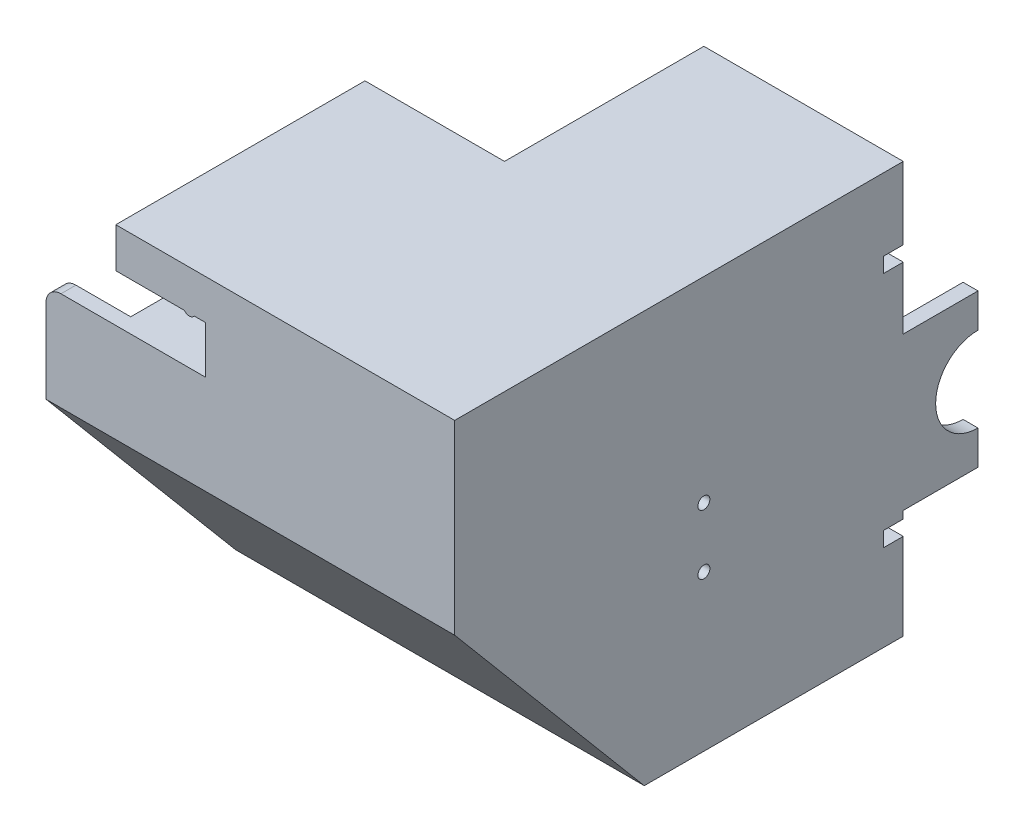
SolidWorks part; units mm, degrees
ref_plane "Front Plane" through (0, 0, 0) normal (0, 0, 1) x (1, 0, 0)
ref_plane "Top Plane" through (0, 0, 0) normal (0, 1, 0) x (1, 0, 0)
ref_plane "Right Plane" through (0, 0, 0) normal (1, 0, 0) x (0, 0, -1)
sketch "Sketch1" plane through (0, 0, 75.0548) normal (0, 0, 1) x (1, 0, 0)
  line L0 (-69.2126, 51.9708) -> (-97.2126, 51.9708)
  line L1 (-97.2126, 51.9708) -> (-97.2126, 43.9708)
  line L2 (-97.2126, 43.9708) -> (-83.4626, 43.9708)
  line L3 (-81.4626, 43.9708) -> (-79.2126, 43.9708)
  line L4 (-79.2126, 43.9708) -> (-79.2126, 34.4708)
  line L5 (-79.2126, 34.4708) -> (-97.2126, 34.4708)
  line L6 (-97.2126, 34.4708) -> (-97.2126, 26.4708)
  line L7 (-97.2126, 26.4708) -> (-69.2126, 26.4708)
  line L8 (-69.2126, 26.4708) -> (-69.2126, 51.9708)
  arc A0 (-83.4626, 43.9708) -> (-81.4626, 43.9708) centre (-82.4626, 44.7208) ccw
  arc A1 (-83.4626, 43.9708) -> (-81.4626, 43.9708) centre (-82.4626, 44.7208) ccw construction
  arc M1 (-83.4626, 43.9708) -> (-81.4626, 43.9708) centre (-82.4626, 44.7208) ccw
  line M2 (-81.4626, 43.9708) -> (-79.2126, 43.9708)
  line M3 (-79.2126, 43.9708) -> (-79.2126, 34.4708)
  line M4 (-79.2126, 34.4708) -> (-97.2126, 34.4708)
  line M5 (-97.2126, 34.4708) -> (-97.2126, 26.4708)
  line M6 (-97.2126, 26.4708) -> (-69.2126, 26.4708)
  line M7 (-69.2126, 26.4708) -> (-69.2126, 51.9708)
  line M8 (-69.2126, 51.9708) -> (-97.2126, 51.9708)
  line M9 (-97.2126, 51.9708) -> (-97.2126, 43.9708)
  line M10 (-97.2126, 43.9708) -> (-83.4626, 43.9708)
extrude "Boss-Extrude1" add sketch "Sketch1" along normal blind 50 contours M10 M1 M2 M3 M4 M5 M6 M7 M8 M9
sketch "Sketch2" plane through (-69.2126, 0, 0) normal (1, 0, 0) x (0, 0, -1)
  line L0 (-125.0548, 51.9708) -> (-35.0548, 51.9708)
  line L1 (-35.0548, 51.9708) -> (-35.0548, 48.9708)
  line L2 (-35.0548, 22.4708) -> (-35.0548, 51.9708) construction
  line L3 (-35.0548, 48.9708) -> (-125.0548, 48.9708)
  line L4 (-125.0548, 26.4708) -> (-125.0548, 51.9708) construction
  line L5 (-125.0548, 48.9708) -> (-125.0548, 51.9708)
  line L6 (-125.0548, 48.9708) -> (-125.0548, 26.4708)
  line L7 (-125.0548, 26.4708) -> (-122.0548, 26.4708)
  line L8 (-125.0548, 26.4708) -> (-75.0548, 26.4708) construction
  line L9 (-122.0548, 26.4708) -> (-122.0548, 48.9708)
  line M3 (-75.0548, 26.4708) -> (-75.0548, 51.9708)
  line M4 (-75.0548, 51.9708) -> (-125.0548, 51.9708)
  line M5 (-125.0548, 51.9708) -> (-125.0548, 26.4708)
  line M6 (-125.0548, 26.4708) -> (-75.0548, 26.4708)
  dimension "D1" = 3
  dimension "D2" = 3
extrude "Boss-Extrude2" add sketch "Sketch2" along normal up to surface (40 mm away) contours L9 L3 M6 M5 | L3 M3 M4 M5 | L3 L1 L0 M3
sketch "Sketch3" plane through (0, 0, 75.0548) normal (0, 0, -1) x (-1, 0, 0)
  line L0 (79.2126, 43.9708) -> (97.2126, 43.9708)
  line L1 (97.2126, 43.9708) -> (97.2126, 34.4708)
  line L2 (97.2126, 34.4708) -> (79.2126, 34.4708)
  line L3 (79.2126, 34.4708) -> (79.2126, 43.9708)
extrude "Cut-Extrude1" cut sketch "Sketch3" against normal blind 30
sketch "Sketch4" plane through (0, 48.9708, 0) normal (0, -1, 0) x (1, 0, 0)
  line L0 (-29.2126, 125.0548) -> (-32.2126, 125.0548)
  line L1 (-97.2126, 125.0548) -> (-29.2126, 125.0548) construction
  line L2 (-32.2126, 125.0548) -> (-32.2126, 35.0548)
  line L3 (-29.2126, 35.0548) -> (-69.2126, 35.0548) construction
  line L4 (-32.2126, 35.0548) -> (-29.2126, 35.0548)
  line L5 (-29.2126, 35.0548) -> (-29.2126, 125.0548)
  dimension "D1" = 3
extrude "Boss-Extrude3" add sketch "Sketch4" along normal up to surface (79.5 mm away)
sketch "Sketch6" plane through (-32.2126, 0, 0) normal (-1, 0, 0) x (0, 0, 1)
  line L0 (125.0548, -30.5292) -> (35.0548, -30.5292)
  line L1 (35.0548, -30.5292) -> (35.0548, -27.5292)
  line L2 (35.0548, -30.5292) -> (35.0548, 48.9708) construction
  line L3 (35.0548, -27.5292) -> (125.0548, -27.5292)
  line L4 (125.0548, -30.5292) -> (125.0548, 26.4708) construction
  line L5 (125.0548, -27.5292) -> (125.0548, -30.5292)
  dimension "D1" = 3
extrude "Boss-Extrude4" add sketch "Sketch6" along normal up to surface (79 mm away)
sketch "Sketch7" plane through (0, 0, 125.0548) normal (0, 0, 1) x (1, 0, 0)
  line L0 (-111.2126, -27.5292) -> (-32.2126, -27.5292)
  line L1 (-32.2126, -27.5292) -> (-32.2126, 26.4708)
  line L2 (-32.2126, 26.4708) -> (-97.2126, 26.4708)
  line L3 (-97.2126, 26.4708) -> (-97.2126, 34.4708)
  line L4 (-97.2126, 34.4708) -> (-111.2126, 34.4708)
  line L5 (-111.2126, 34.4708) -> (-111.2126, -27.5292)
extrude "Boss-Extrude5" add sketch "Sketch7" against normal blind 3
fillet "Fillet1" radius 3 1 edges at (-111.2126, 34.4708, 123.5548)
sketch "Sketch11" plane through (-29.2126, 0, 0) normal (1, 0, 0) x (0, 0, -1)
  line L0 (-35.0548, 34.4708) -> (-39.0548, 34.4708)
  line L1 (-35.0548, 51.9708) -> (-35.0548, -30.5292) construction
  line L2 (-35.0548, 28.4708) -> (-35.0548, 34.4708) construction
  line L3 (-39.0548, 34.4708) -> (-39.0548, 37.4708)
  line L4 (-39.0548, 37.4708) -> (-35.0548, 37.4708)
  line L5 (-35.0548, 37.4708) -> (-35.0548, 34.4708)
  line L6 (-75.0548, 34.4708) -> (-25.0548, 34.4708) construction
  dimension "D1" = 3
  dimension "D2" = 4
extrude "Cut-Extrude2" cut sketch "Sketch11" against normal up to surface (3 mm away) up to face at (-32.2126, 10.7208, 78.5548)
sketch "Sketch12" plane through (0, -30.5292, 0) normal (0, -1, 0) x (1, 0, 0)
  line L0 (-111.2126, 35.0548) -> (-29.2126, 35.0548)
  line L1 (-69.2126, 35.0548) -> (-69.2126, 75.0548)
  line L2 (-70.7126, 39.0548) -> (-67.7126, 39.0548)
  line L3 (-67.7126, 39.0548) -> (-67.7126, 35.0548)
  line L4 (-67.7126, 35.0548) -> (-70.7126, 35.0548)
  line L5 (-70.7126, 35.0548) -> (-70.7126, 39.0548)
  line L6 (-75.2126, 75.0548) -> (-63.2126, 75.0548)
  circle A0 centre (-75.2126, 75.0548) radius 1.2
  circle A1 centre (-63.2126, 75.0548) radius 1.2
  point P10 (-69.2126, 39.0548)
  point P14 (-69.2126, 75.0548)
  dimension "D5" = 2.4
  dimension "D6" = 2.4
  dimension "D1" = 40
  dimension "D2" = 4
  dimension "D3" = 3
  dimension "D4" = 12
sketch "Sketch13" plane through (-29.2126, 0, 0) normal (1, 0, 0) x (0, 0, -1)
  line L0 (-5.0548, 22.4708) -> (-5.0548, -9.1792)
  line L1 (-5.0548, 6.6458) -> (-20.0548, 6.6458)
  line L2 (-5.0548, 22.4708) -> (-35.0548, 22.4708)
  line L3 (-35.0548, 22.4708) -> (-35.0548, -9.1792)
  line L4 (-35.0548, -9.1792) -> (-5.0548, -9.1792)
  line L5 (-20.0548, -9.1792) -> (-20.0548, 22.4708)
  line L6 (-20.0548, 21.9708) -> (-35.0548, 21.9708)
  line L7 (-20.0548, -8.6792) -> (-35.0548, -8.6792)
  circle A0 centre (-20.0548, 6.6458) radius 8.5
  point P9 (-20.0548, 6.6458)
  point P16 (-5.0548, 22.4708)
  dimension "D1" = 17
  dimension "D2" = 15
  dimension "D3" = 0.5
  dimension "D4" = 0.5
extrude "Boss-Extrude6" add sketch "Sketch13" against normal blind 3 contours A0 L5 L6 L3 L7
sketch "Sketch15" plane through (-29.2126, 0, 0) normal (1, 0, 0) x (0, 0, -1)
  line L0 (-35.0548, 22.4708) -> (-35.0548, -9.1792) construction
  line L1 (-35.0548, 6.6458) -> (-75.0548, 6.6458)
  line L6 (-75.0548, 0.6458) -> (-75.0548, 12.6458)
  line L7 (-35.0548, -10.1792) -> (-39.0548, -10.1792)
  line L8 (-35.0548, -8.6792) -> (-35.0548, -30.5292) construction
  line L9 (-39.0548, -10.1792) -> (-39.0548, -13.1792)
  line L10 (-39.0548, -13.1792) -> (-35.0548, -13.1792)
  line L11 (-35.0548, -13.1792) -> (-35.0548, -10.1792)
  line L12 (-20.0548, -8.6792) -> (-35.0548, -8.6792) construction
  circle A0 centre (-75.0548, 0.6458) radius 1.2
  circle A1 centre (-75.0548, 12.6458) radius 1.2
  point P9 (-35.0548, -10.2764)
  point P11 (-75.0548, 6.6458)
  dimension "D2" = 2.4
  dimension "D3" = 2.4
  dimension "D1" = 12
  dimension "D4" = 40
  dimension "D5" = 3
  dimension "D6" = 4
  dimension "D7" = 1.5
extrude "Cut-Extrude3" cut sketch "Sketch15" against normal up to surface (3 mm away)
sketch "Sketch16" plane through (-29.2126, 0, 0) normal (1, 0, 0) x (0, 0, -1)
  line L0 (-125.0548, 16.9708) -> (-85.0548, -30.5292)
  line L1 (-125.0548, 51.9708) -> (-125.0548, -30.5292) construction
  line L2 (-125.0548, -30.5292) -> (-35.0548, -30.5292) construction
  line L3 (-85.0548, -30.5292) -> (-125.0548, -30.5292)
  line L4 (-125.0548, -30.5292) -> (-125.0548, 16.9708)
  line L5 (-35.0548, 51.9708) -> (-125.0548, 51.9708) construction
  dimension "D1" = 35
  dimension "D2" = 40
extrude "Cut-Extrude4" cut sketch "Sketch16" against normal through all
sketch "Sketch17" plane through (-29.2126, 0, 0) normal (1, 0, 0) x (0, 0, -1)
  line L0 (-125.0548, 19.2995) -> (-125.0548, 14.6421)
  line L1 (-125.0548, 14.6421) -> (-87.0158, -30.5292)
  line L2 (-87.0158, -30.5292) -> (-83.0938, -30.5292)
  line L3 (-83.0938, -30.5292) -> (-125.0548, 19.2995)
  point P2 (-85.0548, -30.5292)
  point P4 (-125.0548, 16.9708)
  dimension "D1" = 3
extrude "Boss-Extrude7" add sketch "Sketch17" against normal up to surface (82 mm away) up to face at (-111.2126, -29.0292, 60.6864)
